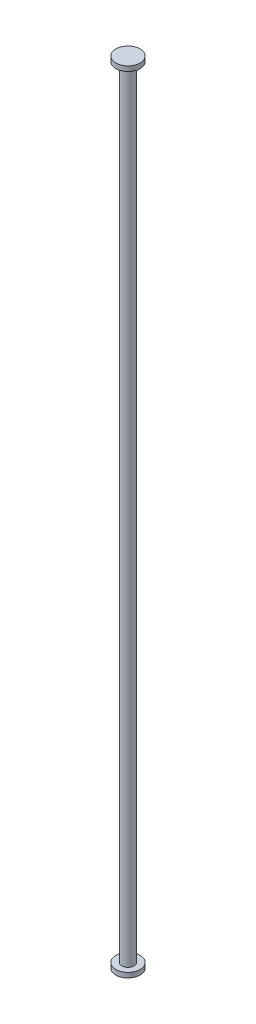
SolidWorks part; units mm, degrees
ref_plane "Front Plane" through (0, 0, 0) normal (0, 0, 1) x (1, 0, 0)
ref_plane "Top Plane" through (0, 0, 0) normal (0, 1, 0) x (1, 0, 0)
ref_plane "Right Plane" through (0, 0, 0) normal (1, 0, 0) x (0, 0, -1)
sketch "Sketch1" plane through (0, 0, 0) normal (0, 1, 0) x (1, 0, 0)
  circle A0 centre (0, 0) radius 2.5
extrude "Boss-Extrude1" add sketch "Sketch1" along normal blind 320
sketch "Sketch2" plane through (0, 0, 0) normal (0, -1, 0) x (1, 0, 0)
  circle A0 centre (0, 0) radius 5
extrude "Boss-Extrude2" add sketch "Sketch2" along normal blind 2
sketch "Sketch3" plane through (0, 320, 0) normal (0, 1, 0) x (1, 0, 0)
  circle A0 centre (0, 0) radius 5
extrude "Boss-Extrude3" add sketch "Sketch3" along normal blind 2
